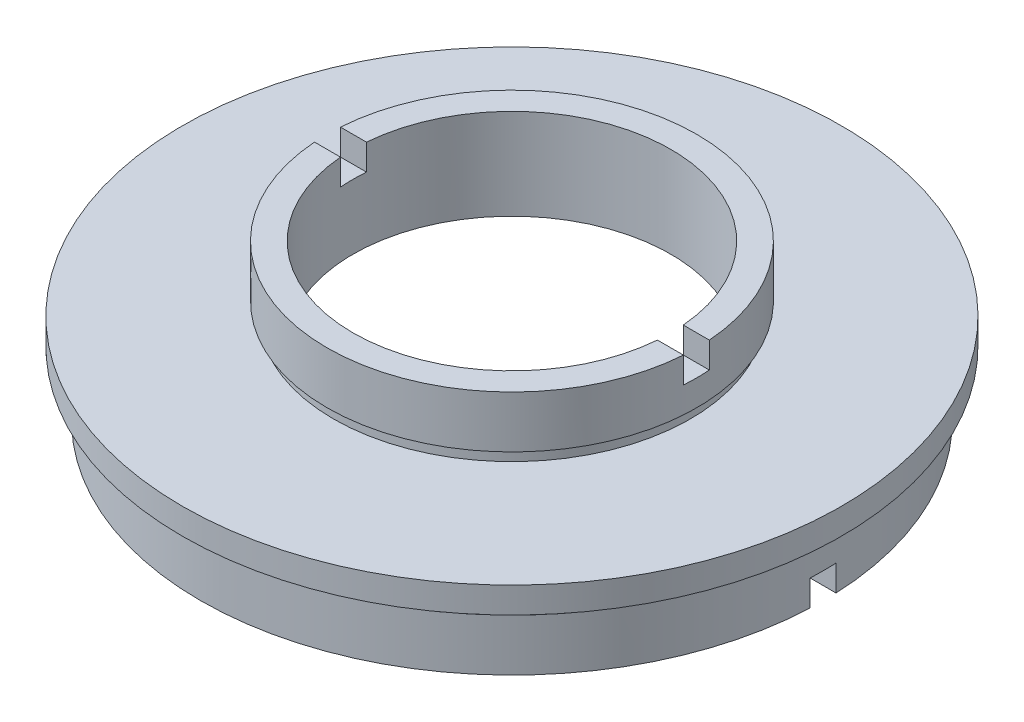
SolidWorks part; units mm, degrees
ref_plane "前视基准面" through (0, 0, 0) normal (0, 0, 1) x (1, 0, 0)
ref_plane "上视基准面" through (0, 0, 0) normal (0, 1, 0) x (1, 0, 0)
ref_plane "右视基准面" through (0, 0, 0) normal (1, 0, 0) x (0, 0, -1)
sketch "草图1" plane through (0, 0, 0) normal (0, 0, 1) x (1, 0, 0)
  line L0 (0, 22.6775) -> (0, 0) construction
  line L1 (-12.25, 12) -> (-14.25, 12)
  line L2 (-14.25, 12) -> (-14.25, 8)
  line L3 (-14.25, 8) -> (-13.75, 8)
  line L4 (-13.75, 8) -> (-13.75, 7)
  line L5 (-13.75, 7) -> (-25.4, 7)
  line L6 (-25.4, 7) -> (-25.4, 5)
  line L7 (-25.4, 5) -> (-23.5, 5)
  line L8 (-23.5, 5) -> (-23.5, 4)
  line L9 (-23.5, 4) -> (-24, 4)
  line L10 (-24, 4) -> (-24, 0)
  line L11 (-24, 0) -> (-20.5, 0)
  line L12 (-20.5, 0) -> (-20.5, 4)
  line L13 (-12.25, 5) -> (-21.1, 5)
  line L14 (-21.1, 5) -> (-21.1, 4)
  line L15 (-21.1, 4) -> (-20.5, 4)
  line L16 (-12.25, 12) -> (-12.25, 5)
  point P3 (-20.8, 4)
  point P5 (-25.4, 6)
  dimension "D2" = 1
  dimension "D3" = 1
  dimension "D4" = 5
  dimension "D5" = 5
  dimension "D6" = 14.25
  dimension "D7" = 25.4
  dimension "D8" = 24
  dimension "D9" = 23.5
  dimension "D10" = 13.75
  dimension "D11" = 20.5
  dimension "D12" = 0
  dimension "D13" = 21.1
  dimension "D14" = 12.25
  dimension "D15" = 12
  dimension "D16" = 7
  dimension "D17" = 1
revolve "旋转1" add sketch "草图1" angle 360 about L0
cosmetic thread "装饰螺纹线1" parameters "D2"=27.5
cosmetic thread "装饰螺纹线2" parameters "D2"=47
cosmetic thread "装饰螺纹线3" parameters "D2"=42
cosmetic thread "装饰螺纹线4" parameters "D2"=25.5
sketch "草图2" plane through (0, 0, 0) normal (1, 0, 0) x (0, 0, -1)
  line L0 (20.5, 12) -> (-20.5, 12) construction
  line L1 (-1, 13.594) -> (1, 13.594)
  line L2 (-1, 13.594) -> (-1, 10)
  line L3 (-1, 10) -> (1, 10)
  line L4 (1, 13.594) -> (1, 10)
  line L5 (-1, 2) -> (1, 2)
  line L6 (-1, 2) -> (-1, -4.6679)
  line L7 (-1, -4.6679) -> (1, -4.6679)
  line L8 (1, 2) -> (1, -4.6679)
  dimension "D1" = 2
  dimension "D2" = 1
  dimension "D3" = 2
  dimension "D4" = 1
  dimension "D5" = 2
  dimension "D6" = 2
extrude "切除-拉伸1" cut sketch "草图2" against normal mid plane 79
